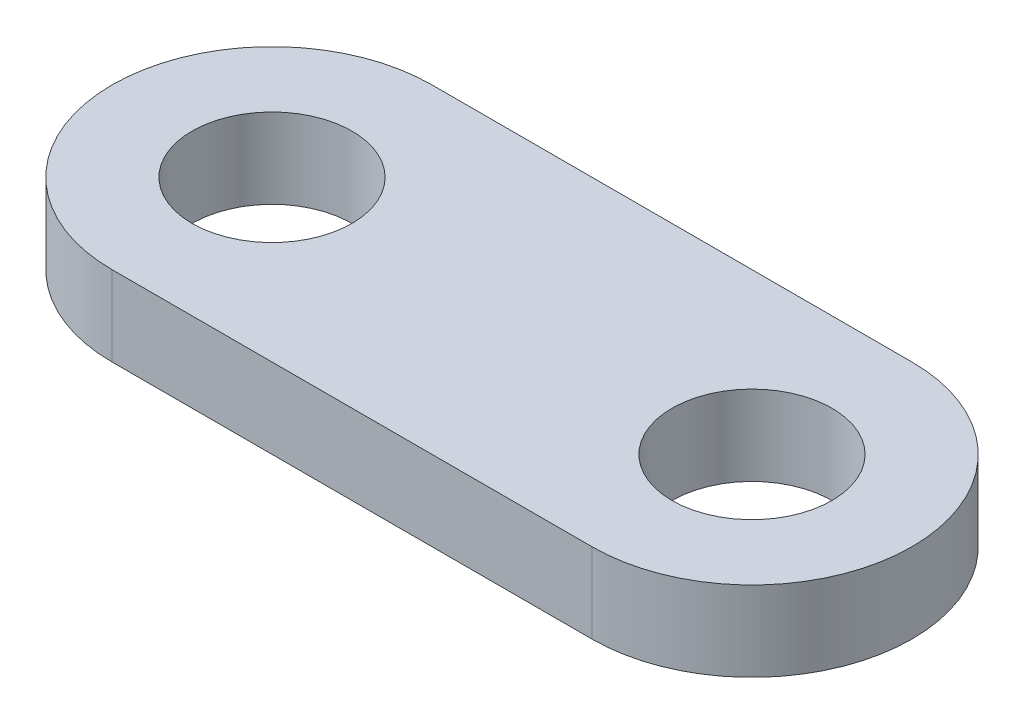
SolidWorks part; units mm, degrees
ref_plane "Front Plane" through (0, 0, 0) normal (0, 0, 1) x (1, 0, 0)
ref_plane "Top Plane" through (0, 0, 0) normal (0, 1, 0) x (1, 0, 0)
ref_plane "Right Plane" through (0, 0, 0) normal (1, 0, 0) x (0, 0, -1)
sketch "Sketch2" plane through (0, 0, 0) normal (0, 1, 0) x (1, 0, 0)
  line L0 (0, 0) -> (30, 0) construction
  line L1 (0, 10) -> (30, 10)
  line L2 (0, -10) -> (30, -10)
  arc A0 (0, 10) -> (0, -10) centre (0, 0) ccw
  arc A1 (30, -10) -> (30, 10) centre (30, 0) ccw
  circle A2 centre (0, 0) radius 5
  circle A3 centre (30, 0) radius 5
  point P3 (15, 0)
  dimension "D2" = 10
  dimension "D3" = 10
  dimension "D4" = 10
  dimension "D1" = 30
extrude "Boss-Extrude1" add sketch "Sketch2" along normal blind 5
